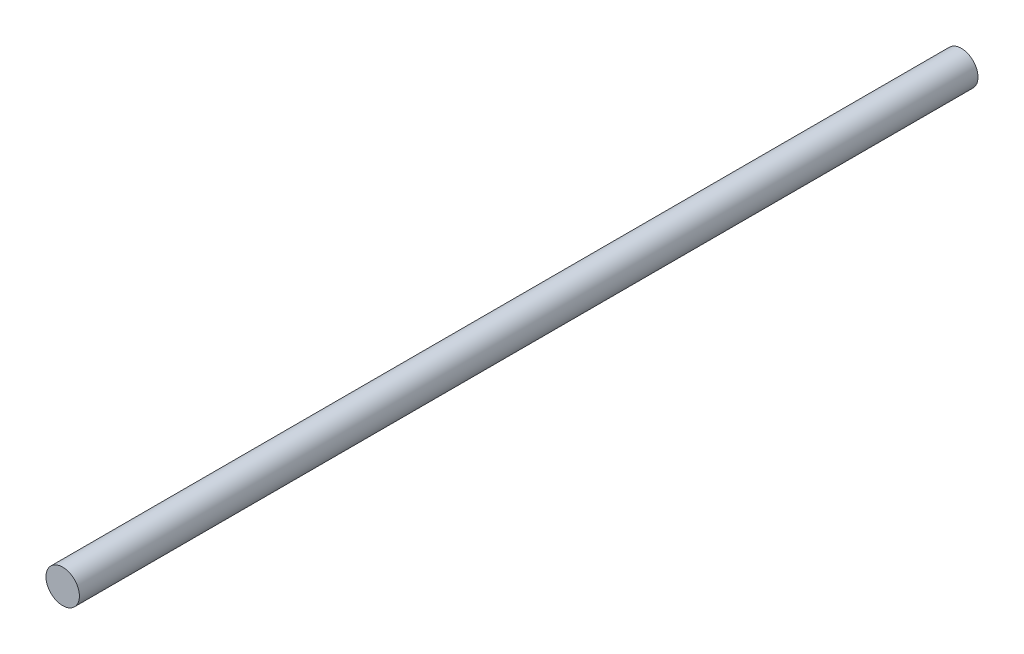
SolidWorks part; units mm, degrees
ref_plane "Front Plane" through (0, 0, 0) normal (0, 0, 1) x (1, 0, 0)
ref_plane "Top Plane" through (0, 0, 0) normal (0, 1, 0) x (1, 0, 0)
ref_plane "Right Plane" through (0, 0, 0) normal (1, 0, 0) x (0, 0, -1)
sketch "Sketch1" plane through (0, 0, 0) normal (0, 0, 1) x (1, 0, 0)
  circle A0 centre (0, 0) radius 5
  dimension "D1" = 10
extrude "Boss-Extrude1" add sketch "Sketch1" along normal blind 269
